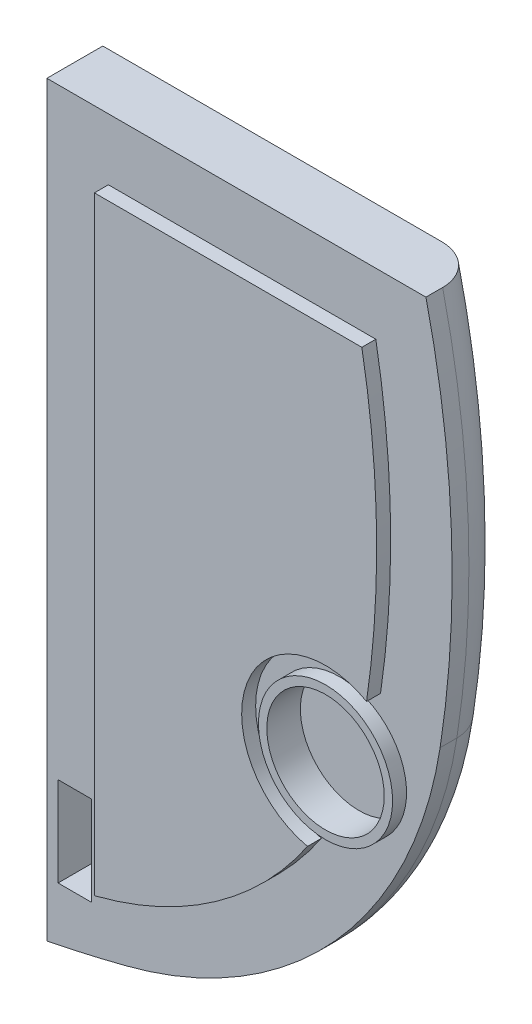
SolidWorks part; units mm, degrees
ref_plane "Front Plane" through (0, 0, 0) normal (0, 0, 1) x (1, 0, 0)
ref_plane "Top Plane" through (0, 0, 0) normal (0, 1, 0) x (1, 0, 0)
ref_plane "Right Plane" through (0, 0, 0) normal (1, 0, 0) x (0, 0, -1)
sketch "Sketch1" plane through (0, 0, 0) normal (0, 0, 1) x (1, 0, 0)
  line L0 (0, 0) -> (67.8, 0)
  line L1 (55, 0) -> (-55, 0) construction
  line L2 (67.8, 0) -> (-107.2, -40.8) construction
  line L3 (70.3411, -68.5271) -> (-4.7487, -56.8001) construction
  line L4 (14.2335, -130.3914) -> (-53.6029, 132.6006) construction
  line L5 (0, 0) -> (0, -133.6573)
  arc A0 (67.8, 0) -> (70.3411, -68.5271) centre (-107.2, -40.8) cw
  arc A1 (70.3411, -68.5271) -> (14.2335, -130.3914) centre (-4.7487, -56.8001) cw
  arc A2 (14.2335, -130.3914) -> (0, -133.6573) centre (-53.6029, 132.6006) cw
  dimension "D4" = 271.6
  dimension "D6" = 22
  dimension "D1" = 67.8
  dimension "D2" = 175
  dimension "D3" = 40.8
  dimension "D5" = 76
extrude "Boss-Extrude1" add sketch "Sketch1" along normal blind 10
fillet "Fillet1" radius 7 3 edges at (7.1387, -132.12, 0) (51.5468, -107.8571, 0) (72.3698, -34.1412, 0)
sketch "Sketch7" plane through (0, 0, 10) normal (0, 0, 1) x (1, 0, 0)
  line L0 (70.3411, -68.5271) -> (52.3411, -68.5271) construction
  line L1 (52.3411, -68.5271) -> (52.3411, -78.5271) construction
  line L4 (11, -11) -> (11, -119.8649)
  line L5 (58.8402, -11) -> (11, -11)
  line L6 (11, -11) -> (11, -119.8649)
  line L7 (58.8402, -11) -> (11, -11)
  arc A0 (59.683, -65.4466) -> (49.119, -93.1769) centre (52.3411, -78.5271) ccw
  arc A6 (11, -119.8649) -> (11.4861, -119.74) centre (-53.6029, 132.6006) ccw
  arc A7 (11.4861, -119.74) -> (59.4729, -66.8297) centre (-4.7487, -56.8001) ccw
  arc A8 (59.4729, -66.8297) -> (58.8402, -11) centre (-107.2, -40.8) ccw
  arc A9 (11, -119.8649) -> (11.4861, -119.74) centre (-53.6029, 132.6006) ccw
  arc A10 (11.4861, -119.74) -> (49.119, -93.1769) centre (-4.7487, -56.8001) ccw
  arc A11 (59.683, -65.4466) -> (58.8402, -11) centre (-107.2, -40.8) ccw
  dimension "D2" = 18
  dimension "D3" = 10
  dimension "D1" = 11
extrude "Boss-Extrude2" add sketch "Sketch7" along normal blind 2.5
sketch "Sketch8" plane through (0, 0, 10) normal (0, 0, 1) x (1, 0, 0)
  line L0 (0, -133.6573) -> (0, -123.6573) construction
  line L1 (0, 0) -> (0, -133.6573) construction
  line L2 (0, -123.6573) -> (2, -123.6573) construction
  line L3 (2, -123.6573) -> (8, -123.6573)
  line L4 (8, -123.6573) -> (8, -107.6573)
  line L5 (8, -107.6573) -> (2, -107.6573)
  line L6 (2, -107.6573) -> (2, -123.6573)
  dimension "D1" = 2
  dimension "D2" = 6
  dimension "D3" = 16
extrude "Cut-Extrude1" cut sketch "Sketch8" against normal blind 6 contours L4 L5 L6 L3
sketch "Sketch9" plane through (0, 0, 10) normal (0, 0, 1) x (1, 0, 0)
  line L0 (41.158, -88.5239) -> (52.3411, -78.5271) construction
  arc A0 (59.683, -65.4466) -> (49.119, -93.1769) centre (52.3411, -78.5271) ccw construction
  circle A1 centre (52.3411, -78.5271) radius 12
extrude "Boss-Extrude3" add sketch "Sketch9" along normal blind 2.5
sketch "Sketch10" plane through (0, 0, 12.5) normal (0, 0, 1) x (1, 0, 0)
  line L0 (59.5856, -68.9606) -> (52.3411, -78.5271) construction
  circle A0 centre (52.3411, -78.5271) radius 12 construction
  circle A1 centre (52.3411, -78.5271) radius 10.5
extrude "Cut-Extrude2" cut sketch "Sketch10" against normal blind 6
